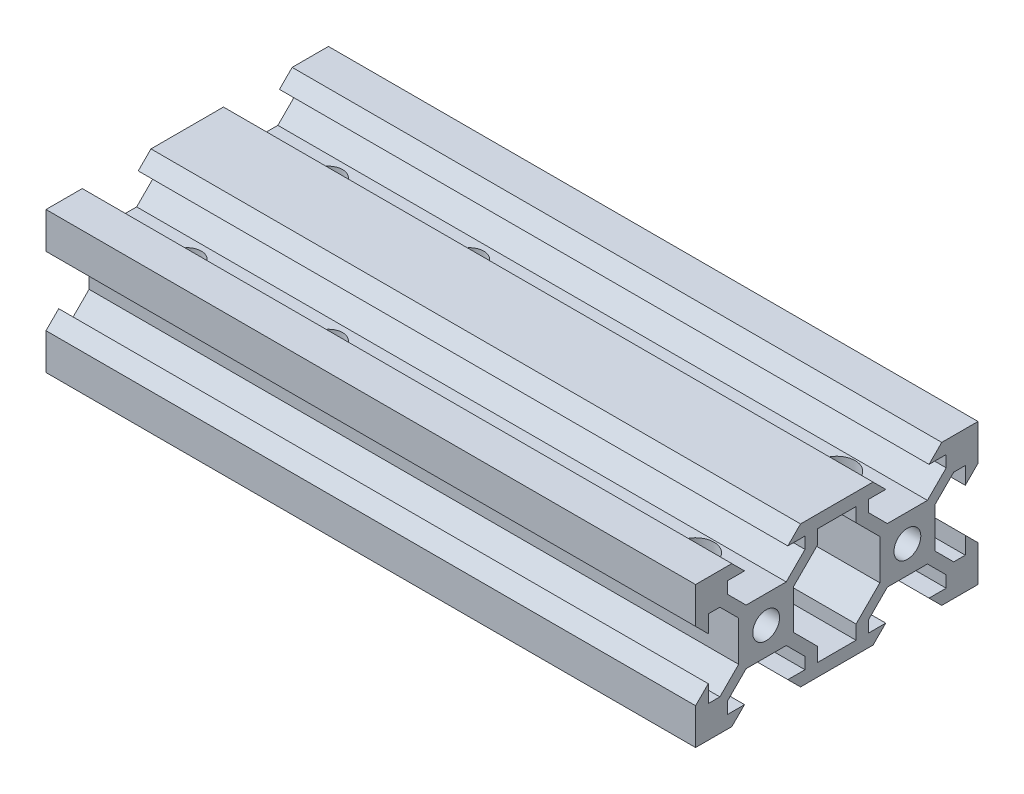
SolidWorks part; units mm, degrees
ref_plane "Front Plane" through (0, 0, 0) normal (0, 0, 1) x (1, 0, 0)
ref_plane "Top Plane" through (0, 0, 0) normal (0, 1, 0) x (1, 0, 0)
ref_plane "Right Plane" through (0, 0, 0) normal (1, 0, 0) x (0, 0, -1)
sketch "Sketch1" plane through (0, 0, 0) normal (0, 1, 0) x (1, 0, 0)
  line L1 (-46, -20) -> (46, -20)
  line L2 (-46, -20) -> (-46, 20)
  line L3 (-46, 20) -> (46, 20)
  line L4 (46, -20) -> (46, 20)
  line L5 (0, 20) -> (0, -20) construction
  line L6 (-46, 0) -> (46, 0) construction
  point P0 (0, 0)
  dimension "D1" = 92
  dimension "D2" = 40
extrude "Boss-Extrude1" add sketch "Sketch1" along normal blind 20
sketch "Sketch7" plane through (46, 0, 0) normal (1, 0, 0) x (0, 0, -1)
  line L0 (-20, 0) -> (20, 0) construction
  line L1 (-20, 20) -> (20, 20) construction
  line L2 (-20, 20) -> (-20, 0) construction
  line L3 (-20, 0) -> (20, 0) construction
  line L4 (0, 20) -> (0, 0) construction
  line L5 (-7.1593, 13.9) -> (-4.4993, 16.56)
  line L12 (-12.8393, 13.9) -> (-7.1593, 13.9)
  line L14 (-12.8393, 13.9) -> (-15.4993, 16.56)
  line L15 (-4.4993, 16.56) -> (-4.4993, 18.2)
  line L20 (-15.4993, 16.56) -> (-15.4993, 18.2)
  line L21 (-4.4993, 18.2) -> (-6.9343, 18.2)
  line L22 (-13.0643, 18.2) -> (-14.8643, 20)
  line L23 (-15.4993, 18.2) -> (-13.0643, 18.2)
  line L24 (-18.2, 13.0643) -> (-20, 14.8643)
  line L25 (-20, 20) -> (-20, 14.8643)
  line L26 (-6.9343, 18.2) -> (-5.1343, 20)
  line L27 (-18.2, 13.0643) -> (-18.2, 15.4993)
  line L28 (-18.2, 15.4993) -> (-16.56, 15.4993)
  line L29 (-16.56, 15.4993) -> (-13.9, 12.8393)
  line L30 (-14.8643, 20) -> (-20, 20)
  line L31 (-13.9, 12.8393) -> (-13.9, 7.1593)
  line L36 (-6.0987, 12.8393) -> (-6.0987, 7.1593)
  line L37 (-4.4993, 16.56) -> (-7.1593, 13.9) [skipped]
  line L38 (-6.0987, 12.8393) -> (-3.4387, 15.4993) [skipped]
  line L39 (-3.4387, 15.4993) -> (-1.7987, 15.4993) [skipped]
  line L40 (-1.7987, 15.4993) -> (-1.7987, 13.0643) [skipped]
  line L41 (-1.7987, 13.0643) -> (0.0013, 14.8643) [skipped]
  line L42 (0.0013, 14.8643) -> (0.0013, 20) [skipped]
  line L43 (0.0013, 20) -> (-5.1343, 20) [skipped]
  line L44 (-6.9343, 18.2) -> (-5.1343, 20) [skipped]
  line L45 (-6.9343, 18.2) -> (-4.4993, 18.2) [skipped]
  line L46 (-4.4993, 18.2) -> (-4.4993, 16.56) [skipped]
  line L48 (-6.0987, 7.1593) -> (-2.73, 3.7907)
  line L49 (-7.1593, 6.0987) -> (-4.4993, 3.4387)
  line L50 (-4.4993, 3.4387) -> (-4.4993, 1.7987)
  line L51 (-4.4993, 1.7987) -> (-6.9343, 1.7987)
  line L52 (-6.9343, 1.7987) -> (-5.1343, -0.0013)
  line L54 (-5.1343, 20) -> (5.1343, 20)
  line L58 (-2.73, 18.2) -> (2.73, 18.2)
  line L59 (-15.4993, 3.4387) -> (-12.8393, 6.0987)
  line L60 (-13.9, 7.1593) -> (-16.56, 4.4993)
  line L61 (-16.56, 4.4993) -> (-18.2, 4.4993)
  line L62 (-18.2, 4.4993) -> (-18.2, 6.9343)
  line L63 (-18.2, 6.9343) -> (-20, 5.1343)
  line L64 (-20, 5.1343) -> (-20, -0.0013)
  line L65 (-20, -0.0013) -> (-14.8643, -0.0013)
  line L66 (-13.0643, 1.7987) -> (-14.8643, -0.0013)
  line L67 (-13.0643, 1.7987) -> (-15.4993, 1.7987)
  line L68 (-15.4993, 1.7987) -> (-15.4993, 3.4387)
  line L69 (-6.0987, 12.8393) -> (-2.73, 16.208)
  line L70 (-12.8393, 6.0987) -> (-7.1593, 6.0987)
  line L71 (-3.4387, 4.4993) -> (-6.0987, 7.1593) [skipped]
  line L72 (-1.7987, 4.4993) -> (-3.4387, 4.4993) [skipped]
  line L73 (-1.7987, 6.9343) -> (0.0013, 5.1343) [skipped]
  line L74 (-1.7987, 6.9343) -> (-1.7987, 4.4993) [skipped]
  line L87 (-2.73, 16.208) -> (-2.73, 18.2)
  line L88 (-2.73, 3.7907) -> (-2.73, 1.7987)
  line L113 (0.0013, -0.0013) -> (0.0013, 5.1343) [skipped]
  line L114 (-5.1343, -0.0013) -> (0.0013, -0.0013) [skipped]
  line L115 (-2.73, 1.7987) -> (2.73, 1.7987)
  line L116 (-5.1343, -0.0013) -> (0, 0)
  line L117 (20, 20) -> (20, 0) construction
  line L118 (5.1343, -0.0013) -> (0, 0)
  line L119 (2.73, 3.7907) -> (2.73, 1.7987)
  line L120 (2.73, 16.208) -> (2.73, 18.2)
  line L121 (12.8393, 6.0987) -> (7.1593, 6.0987)
  line L122 (6.0987, 12.8393) -> (2.73, 16.208)
  line L123 (15.4993, 1.7987) -> (15.4993, 3.4387)
  line L124 (13.0643, 1.7987) -> (15.4993, 1.7987)
  line L125 (13.0643, 1.7987) -> (14.8643, -0.0013)
  line L126 (20, -0.0013) -> (14.8643, -0.0013)
  line L127 (20, 5.1343) -> (20, -0.0013)
  line L128 (18.2, 6.9343) -> (20, 5.1343)
  line L129 (18.2, 4.4993) -> (18.2, 6.9343)
  line L130 (16.56, 4.4993) -> (18.2, 4.4993)
  line L131 (13.9, 7.1593) -> (16.56, 4.4993)
  line L132 (15.4993, 3.4387) -> (12.8393, 6.0987)
  line L133 (6.9343, 1.7987) -> (5.1343, -0.0013)
  line L134 (4.4993, 1.7987) -> (6.9343, 1.7987)
  line L135 (4.4993, 3.4387) -> (4.4993, 1.7987)
  line L136 (7.1593, 6.0987) -> (4.4993, 3.4387)
  line L137 (6.0987, 7.1593) -> (2.73, 3.7907)
  line L138 (6.0987, 12.8393) -> (6.0987, 7.1593)
  line L139 (13.9, 12.8393) -> (13.9, 7.1593)
  line L140 (14.8643, 20) -> (20, 20)
  line L141 (16.56, 15.4993) -> (13.9, 12.8393)
  line L142 (18.2, 15.4993) -> (16.56, 15.4993)
  line L143 (18.2, 13.0643) -> (18.2, 15.4993)
  line L144 (6.9343, 18.2) -> (5.1343, 20)
  line L145 (20, 20) -> (20, 14.8643)
  line L146 (18.2, 13.0643) -> (20, 14.8643)
  line L147 (15.4993, 18.2) -> (13.0643, 18.2)
  line L148 (13.0643, 18.2) -> (14.8643, 20)
  line L149 (4.4993, 18.2) -> (6.9343, 18.2)
  line L150 (15.4993, 16.56) -> (15.4993, 18.2)
  line L151 (4.4993, 16.56) -> (4.4993, 18.2)
  line L152 (12.8393, 13.9) -> (15.4993, 16.56)
  line L153 (12.8393, 13.9) -> (7.1593, 13.9)
  line L154 (7.1593, 13.9) -> (4.4993, 16.56)
  circle A0 centre (-10, 10) radius 1.9
  circle A1 centre (10, 10) radius 1.9
  point P36 (0, 1.7987)
  point P81 (-9.9993, 9.9993)
  point P84 (0, 18.2)
  point P103 (9.9993, 9.9993)
  line M26 (-20, 0) -> (20, 0)
  line M27 (20, 0) -> (20, 20)
  line M28 (20, 20) -> (-20, 20)
  line M29 (-20, 20) -> (-20, 0)
  dimension "D1" = 4.3
  dimension "D11" = 3.8
  dimension "D2" = 6.13
  dimension "D3" = 11
  dimension "D4" = 4.3
  dimension "D5" = 4.3
  dimension "D6" = 1.8
  dimension "D7" = 1.8
  dimension "D8" = 1.5
  dimension "D9" = 1.5
  dimension "D12" = 1.5
  dimension "D13" = 5.68
  dimension "D10" = 4
extrude "Cut-Extrude13" cut sketch "Sketch7" against normal through all contours L21 L26 L22 L23 L20 L14 L12 L5 L15 M28 | L63 L62 L61 L60 L31 L29 L28 L27 L24 M29 | L70 L59 L68 L67 L66 L52 L51 L50 L49 M26 | L138 L122 L120 L58 L87 L69 L36 L48 L88 L115 L119 L137 | L121 L136 L135 L134 L133 L125 L124 L123 L132 M26 | L146 L143 L142 L141 L139 L131 L130 L129 L128 M27 | L154 L153 L152 L150 L147 L148 L144 L149 L151 M28 | A0 | A1
sketch "Sketch16" plane through (0, 13.9, 0) normal (0, 1, 0) x (1, 0, 0)
  line L4 (46, 12.8393) -> (46, 7.1593) construction
  line L5 (46, -12.8393) -> (46, -7.1593) construction
  circle A0 centre (36, -9.9993) radius 2.6
  circle A1 centre (36, 9.9993) radius 2.6
  dimension "D1" = 5.2
  dimension "D2" = 5.2
  dimension "D3" = 10
  dimension "D4" = 10
extrude "Cut-Extrude11" cut sketch "Sketch16" against normal through all
ref_plane "Plane1" through (0, 0, 0) normal (-1, 0, 0) x (0, 0, 1)
sketch "Sketch17" plane through (0, 13.9, 0) normal (0, 1, 0) x (1, 0, 0)
  line L0 (-46, -12.8393) -> (-46, -7.1593) construction
  line L1 (-46, 12.8393) -> (-46, 7.1593) construction
  circle A0 centre (-36, -9.9993) radius 2
  circle A1 centre (-16, -9.9993) radius 2
  circle A2 centre (-36, 9.9993) radius 2
  circle A3 centre (-16, 9.9993) radius 2
  dimension "D5" = 4
  dimension "D1" = 10
  dimension "D2" = 10
  dimension "D3" = 20
  dimension "D4" = 20
extrude "Cut-Extrude14" cut sketch "Sketch17" against normal through all
